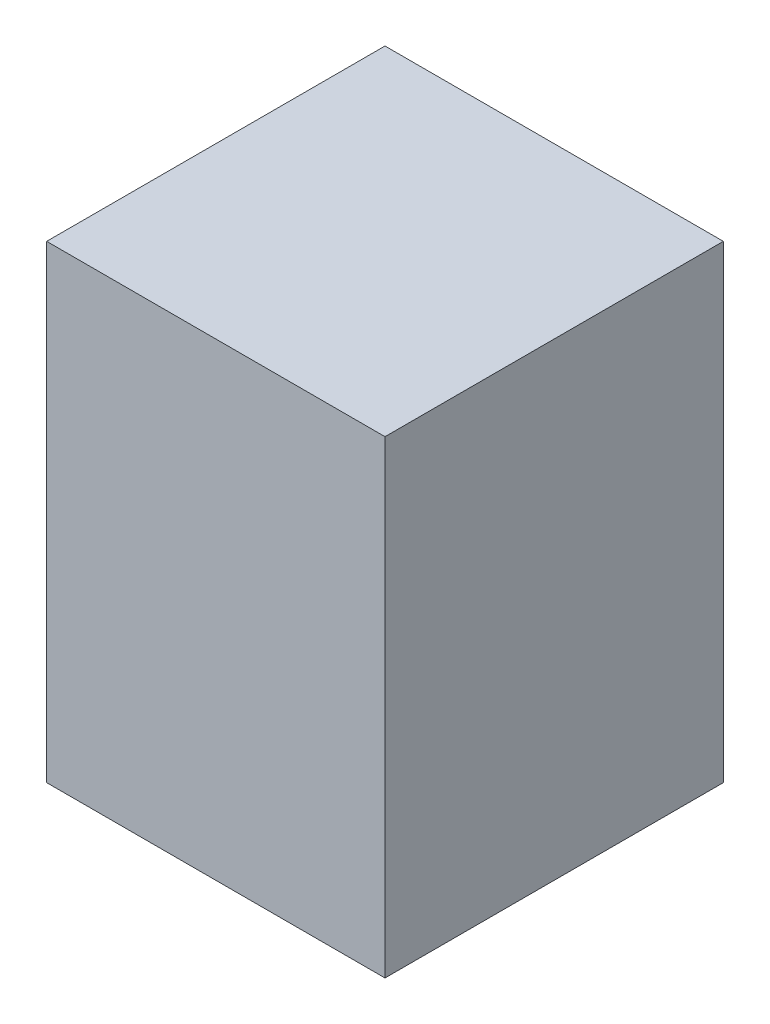
SolidWorks part; units mm, degrees
ref_plane "Front Plane" through (0, 0, 0) normal (0, 0, 1) x (1, 0, 0)
ref_plane "Top Plane" through (0, 0, 0) normal (0, 1, 0) x (1, 0, 0)
ref_plane "Right Plane" through (0, 0, 0) normal (1, 0, 0) x (0, 0, -1)
sketch "Sketch1" plane through (0, 0, 0) normal (0, 1, 0) x (1, 0, 0)
  line L1 (-9.75, 0) -> (0, 0)
  line L2 (-9.75, 0) -> (-9.75, -9.75)
  line L3 (-9.75, -9.75) -> (0, -9.75)
  line L4 (0, 0) -> (0, -9.75)
  point P4 (0, 0)
  dimension "D1" = 9.75
extrude "Boss-Extrude1" add sketch "Sketch1" along normal blind 13.51
